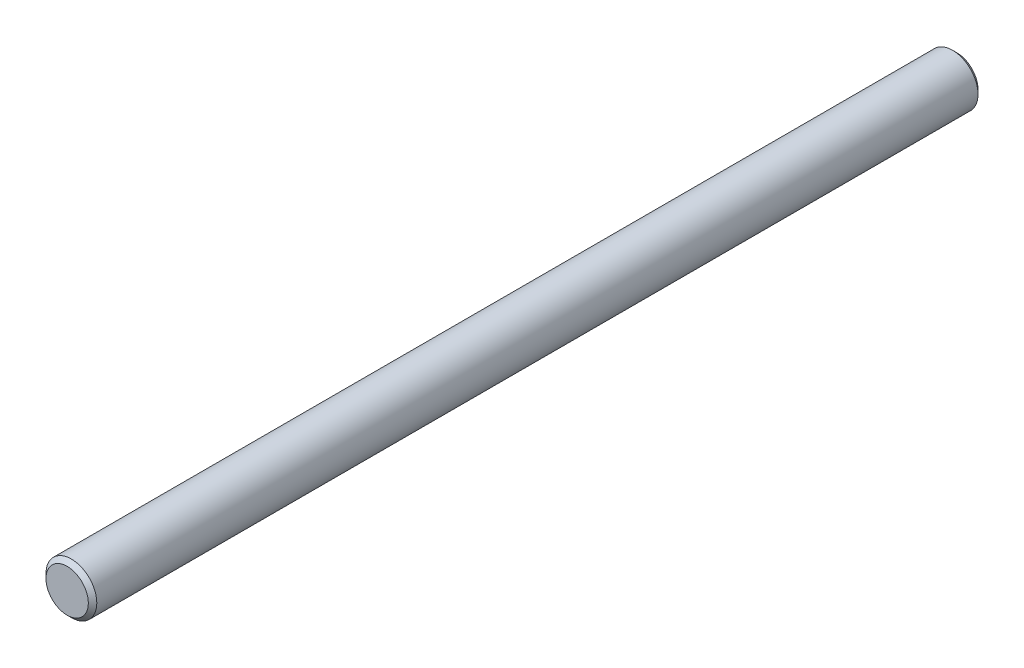
SolidWorks part; units mm, degrees
material "AISI 304"
ref_plane "Спереди" through (0, 0, 0) normal (0, 0, 1) x (1, 0, 0)
ref_plane "Сверху" through (0, 0, 0) normal (0, 1, 0) x (1, 0, 0)
ref_plane "Справа" through (0, 0, 0) normal (1, 0, 0) x (0, 0, -1)
sketch "Эскиз1" plane through (0, 0, 0) normal (0, 0, 1) x (1, 0, 0)
  circle A0 centre (0, 0) radius 6
  dimension "D1" = 12
extrude "Бобышка-Вытянуть1" add sketch "Эскиз1" along normal blind 210
chamfer "Фаска1" distance 1 angle 45 2 edges at (6, 0, 0) (6, 0, 210)
